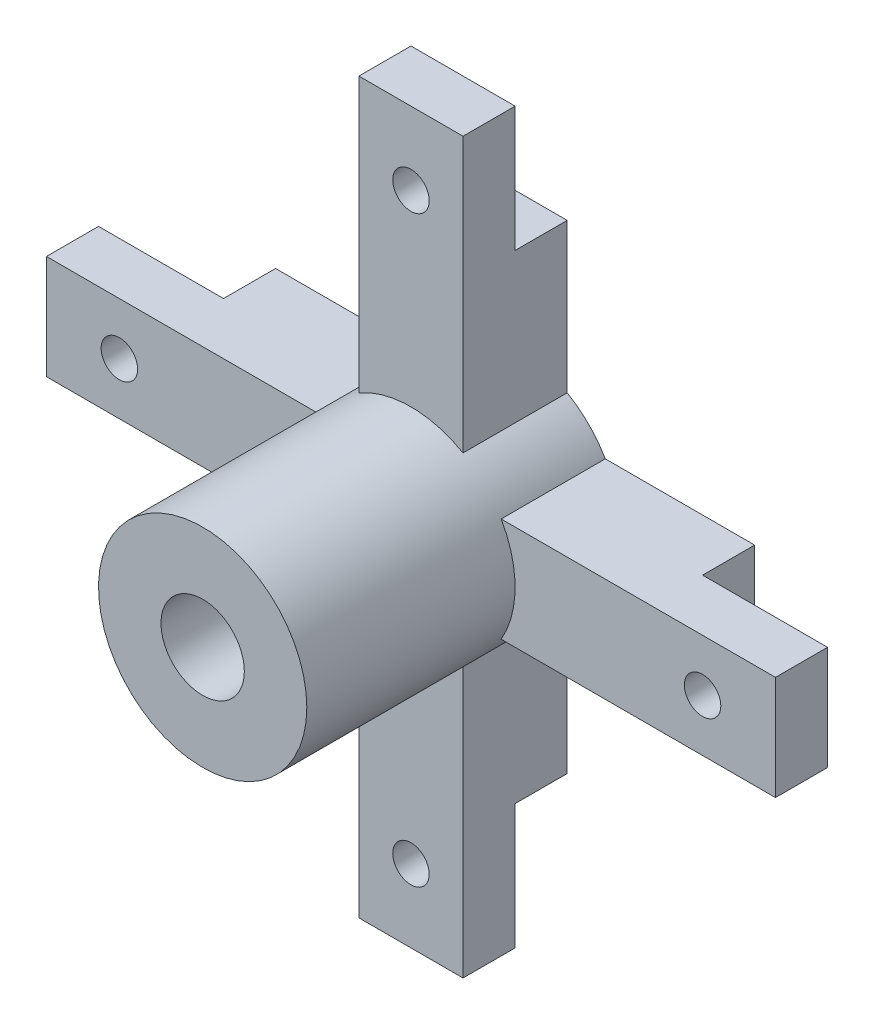
SolidWorks part; units mm, degrees
ref_plane "Спереди" through (0, 0, 0) normal (0, 0, 1) x (1, 0, 0)
ref_plane "Сверху" through (0, 0, 0) normal (0, 1, 0) x (1, 0, 0)
ref_plane "Справа" through (0, 0, 0) normal (1, 0, 0) x (0, 0, -1)
sketch "Эскиз1" plane through (0, 0, 0) normal (0, 0, 1) x (1, 0, 0)
  circle A0 centre (0, 0) radius 4
  circle A1 centre (0, 0) radius 10
  dimension "D1" = 8
  dimension "D2" = 20
extrude "Бобышка-Вытянуть1" add sketch "Эскиз1" along normal blind 30
sketch "Эскиз2" plane through (0, 0, 0) normal (0, 0, -1) x (-1, 0, 0)
  line L1 (-5, 4) -> (5, 4)
  line L2 (-5, 4) -> (-5, 35)
  line L3 (-5, 35) -> (5, 35)
  line L4 (5, 4) -> (5, 35)
  line L5 (-5, 4) -> (5, 35) construction
  line L6 (-5, 35) -> (5, 4) construction
  circle A0 centre (0, 0) radius 4 construction
  point P0 (0, 19.5)
  point P8 (0, 4)
  dimension "D1" = 35
  dimension "D2" = 10
extrude "Бобышка-Вытянуть2" add sketch "Эскиз2" against normal blind 10
sketch "Эскиз3" plane through (0, 0, 0) normal (0, 0, -1) x (-1, 0, 0)
  line L0 (-5, 35) -> (-5, 8.6603) construction
  line L1 (-5, 23) -> (5, 23)
  line L2 (-5, 23) -> (-5, 35)
  line L3 (-5, 35) -> (5, 35)
  line L4 (5, 23) -> (5, 35)
  line L5 (-5, 23) -> (5, 35) construction
  line L6 (-5, 35) -> (5, 23) construction
  point P0 (0, 29)
  dimension "D1" = 23
extrude "Вырез-Вытянуть1" cut sketch "Эскиз3" against normal blind 5
hole_wizard "Диаметр отверстия Ø3.5 (3.5)1" positions "Эскиз4" profile "Эскиз5" hole size "Ø3.5" standard "DIN" end condition through all
sketch "Эскиз4" plane through (0, 0, 5) normal (0, 0, -1) x (-1, 0, 0)
  point P0 (0, 28)
  dimension "D1" = 28
sketch "Эскиз5" plane through (0, 28, 5) normal (1, 0, 0) x (0, 1, 0)
  line L0 (0, 0) -> (0, 25)
  line L1 (0, 25) -> (1.75, 25)
  line L2 (1.75, 25) -> (1.75, 0)
  line L5 (1.75, 0) -> (0, 0)
  line L11 (0, -6.35) -> (0, 107.95) construction
  dimension "Диаметр сквозного отверстия" = 3.5
  dimension "Глубина сквозного отверстия" = 25
pattern_circular "Круговой массив1" count 4 over 360 about axis through (0, 0, 0) along (0, 0, 1) of "Бобышка-Вытянуть2", "Вырез-Вытянуть1", "Диаметр отверстия Ø3.5 (3.5)1"
